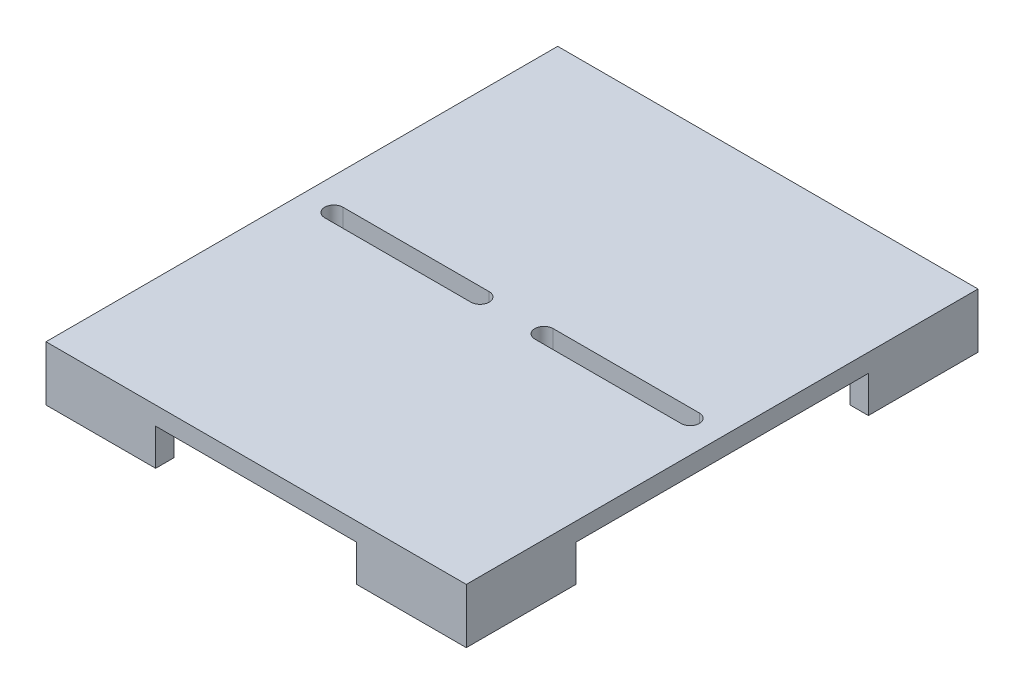
SolidWorks part; units mm, degrees
material "AISI 1020 Steel, Cold Rolled"
ref_plane "Front Plane" through (0, 0, 0) normal (0, 0, 1) x (1, 0, 0)
ref_plane "Top Plane" through (0, 0, 0) normal (0, 1, 0) x (1, 0, 0)
ref_plane "Right Plane" through (0, 0, 0) normal (1, 0, 0) x (0, 0, -1)
sketch "Sketch1" plane through (0, 0, 0) normal (0, 1, 0) x (1, 0, 0)
  line L0 (69.85, 139.7) -> (69.85, 152.4)
  line L1 (-107.95, -139.7) -> (107.95, -139.7)
  line L2 (-107.95, -139.7) -> (-107.95, 139.7)
  line L3 (-107.95, 139.7) -> (107.95, 139.7)
  line L4 (107.95, -139.7) -> (107.95, 139.7)
  line L5 (-107.95, -139.7) -> (107.95, 139.7) construction
  line L6 (-107.95, 139.7) -> (107.95, -139.7) construction
  line L7 (69.85, 101.6) -> (146.05, 101.6) construction
  line L8 (69.85, 101.6) -> (69.85, 177.8) construction
  line L9 (69.85, 177.8) -> (146.05, 177.8) construction
  line L10 (146.05, 101.6) -> (146.05, 177.8) construction
  line L11 (69.85, 101.6) -> (146.05, 177.8) construction
  line L12 (69.85, 177.8) -> (146.05, 101.6) construction
  line L13 (69.85, 152.4) -> (120.65, 152.4)
  line L14 (120.65, 152.4) -> (120.65, 101.6)
  line L15 (120.65, 101.6) -> (107.95, 101.6)
  line L16 (0, 139.7) -> (0, -139.7) construction
  line L17 (-107.95, 0) -> (107.95, 0) construction
  line L18 (-120.65, 101.6) -> (-107.95, 101.6)
  line L19 (-120.65, 152.4) -> (-120.65, 101.6)
  line L20 (-69.85, 152.4) -> (-120.65, 152.4)
  line L21 (-69.85, 139.7) -> (-69.85, 152.4)
  line L22 (120.65, -101.6) -> (107.95, -101.6)
  line L23 (120.65, -152.4) -> (120.65, -101.6)
  line L24 (69.85, -152.4) -> (120.65, -152.4)
  line L25 (69.85, -139.7) -> (69.85, -152.4)
  line L26 (-69.85, -139.7) -> (-69.85, -152.4)
  line L27 (-69.85, -152.4) -> (-120.65, -152.4)
  line L28 (-120.65, -152.4) -> (-120.65, -101.6)
  line L29 (-120.65, -101.6) -> (-107.95, -101.6)
  line L30 (-146.05, -177.8) -> (-146.05, 177.8)
  line L31 (-146.05, 177.8) -> (146.05, 177.8)
  line L32 (146.05, -177.8) -> (146.05, 177.8)
  line L33 (-146.05, -177.8) -> (146.05, -177.8)
  point P0 (0, 0)
  dimension "D1" = 279.4
  dimension "D2" = 215.9
  dimension "D3" = 76.2
  dimension "D4" = 76.2
  dimension "D5" = 12.7
  dimension "D6" = 12.7
  dimension "D7" = 38.1
extrude "Boss-Extrude1" add sketch "Sketch1" along normal blind 12.7 contours L30 L33 L32 L31 L28 L29 L2 L18 L19 L20 L21 L3 L0 L13 L14 L15 L4 L22 L23 L24 L25 L1 L26 L27 | L3 L21 L20 L19 L18 L2 | L29 L28 L27 L26 L1 L2 | L1 L4 L3 L2 | L1 L25 L24 L23 L22 L4 | L15 L14 L13 L0 L3 L4
sketch "Sketch2" plane through (0, 12.7, 0) normal (0, 1, 0) x (1, 0, 0)
  line L0 (0, 0) -> (-146.05, 0) construction
  line L1 (-146.05, -177.8) -> (-146.05, 177.8) construction
  line L2 (-123.825, 0) -> (-22.225, 0) construction
  line L3 (-123.825, 6.35) -> (-22.225, 6.35)
  line L4 (-123.825, -6.35) -> (-22.225, -6.35)
  line L5 (0, -139.7) -> (0, 139.7) construction
  line L6 (123.825, 0) -> (22.225, 0) construction
  line L7 (123.825, 6.35) -> (22.225, 6.35)
  line L8 (123.825, -6.35) -> (22.225, -6.35)
  arc A0 (-123.825, 6.35) -> (-123.825, -6.35) centre (-123.825, 0) ccw
  arc A1 (-22.225, -6.35) -> (-22.225, 6.35) centre (-22.225, 0) ccw
  arc A2 (123.825, 6.35) -> (123.825, -6.35) centre (123.825, 0) cw
  arc A3 (22.225, -6.35) -> (22.225, 6.35) centre (22.225, 0) cw
  point P7 (-73.025, 0)
  point P16 (0, 0)
  point P18 (73.025, 0)
  dimension "D1" = 101.6
  dimension "D2" = 12.7
extrude "Cut-Extrude1" cut sketch "Sketch2" against normal through all
sketch "Sketch3" plane through (0, 0, 0) normal (0, -1, 0) x (1, 0, 0)
  line L0 (-69.85, 139.7) -> (-69.85, 152.4) construction
  line L1 (-146.05, 177.8) -> (146.05, 177.8) construction
  line L2 (-146.05, 177.8) -> (-146.05, -177.8) construction
  line L3 (146.05, 177.8) -> (146.05, -177.8) construction
  line L4 (-146.05, -177.8) -> (146.05, -177.8) construction
  line L5 (-146.05, 177.8) -> (146.05, 177.8)
  line L6 (-146.05, 177.8) -> (-146.05, -177.8)
  line L7 (146.05, 177.8) -> (146.05, -177.8)
  line L8 (-146.05, -177.8) -> (146.05, -177.8)
  line L9 (-133.35, 165.1) -> (-133.35, -165.1)
  line L10 (-133.35, -165.1) -> (133.35, -165.1)
  line L11 (133.35, 165.1) -> (133.35, -165.1)
  line L12 (-133.35, 165.1) -> (133.35, 165.1)
  line L14 (-146.05, -101.6) -> (146.05, -101.6)
  line L15 (-146.05, -101.6) -> (-146.05, 101.6)
  line L16 (-146.05, 101.6) -> (146.05, 101.6)
  line L17 (146.05, -101.6) -> (146.05, 101.6)
  line L18 (-146.05, -101.6) -> (146.05, 101.6) construction
  line L19 (-146.05, 101.6) -> (146.05, -101.6) construction
  line L20 (-69.85, -177.8) -> (69.85, -177.8)
  line L21 (-69.85, -177.8) -> (-69.85, 177.8)
  line L22 (-69.85, 177.8) -> (69.85, 177.8)
  line L23 (69.85, -177.8) -> (69.85, 177.8)
  line L24 (-69.85, -177.8) -> (69.85, 177.8) construction
  line L25 (-69.85, 177.8) -> (69.85, -177.8) construction
  point P9 (0, 0)
  point P15 (0, 0)
  line M17 (-146.05, 177.8) -> (-146.05, -177.8)
  line M18 (-146.05, -177.8) -> (146.05, -177.8)
  line M19 (146.05, -177.8) -> (146.05, 177.8)
  line M20 (146.05, 177.8) -> (-146.05, 177.8)
  dimension "D1" = 12.7
extrude "Boss-Extrude2" add sketch "Sketch3" along normal blind 25.4 contours L12 L21 L5 L16 L9 M17 | L23 L12 L11 L16 M19 M20 | L23 L14 L11 L10 M18 M19 | L21 L10 L9 L14 L6 M18
sketch "Sketch4" plane through (0, -25.4, 0) normal (0, -1, 0) x (1, 0, 0)
  line L0 (-146.05, 101.6) -> (-133.35, 101.6)
  line L1 (-133.35, 101.6) -> (-133.35, 165.1)
  line L2 (-133.35, 165.1) -> (-69.85, 165.1)
  line L3 (-69.85, 165.1) -> (-69.85, 177.8)
  line L4 (-69.85, 177.8) -> (-146.05, 177.8)
  line L5 (-146.05, 177.8) -> (-146.05, 101.6)
sketch "Sketch5" plane through (146.05, 0, 0) normal (1, 0, 0) x (0, 0, -1)
  circle A0 centre (-161.2251, -15.6417) radius 6.35
